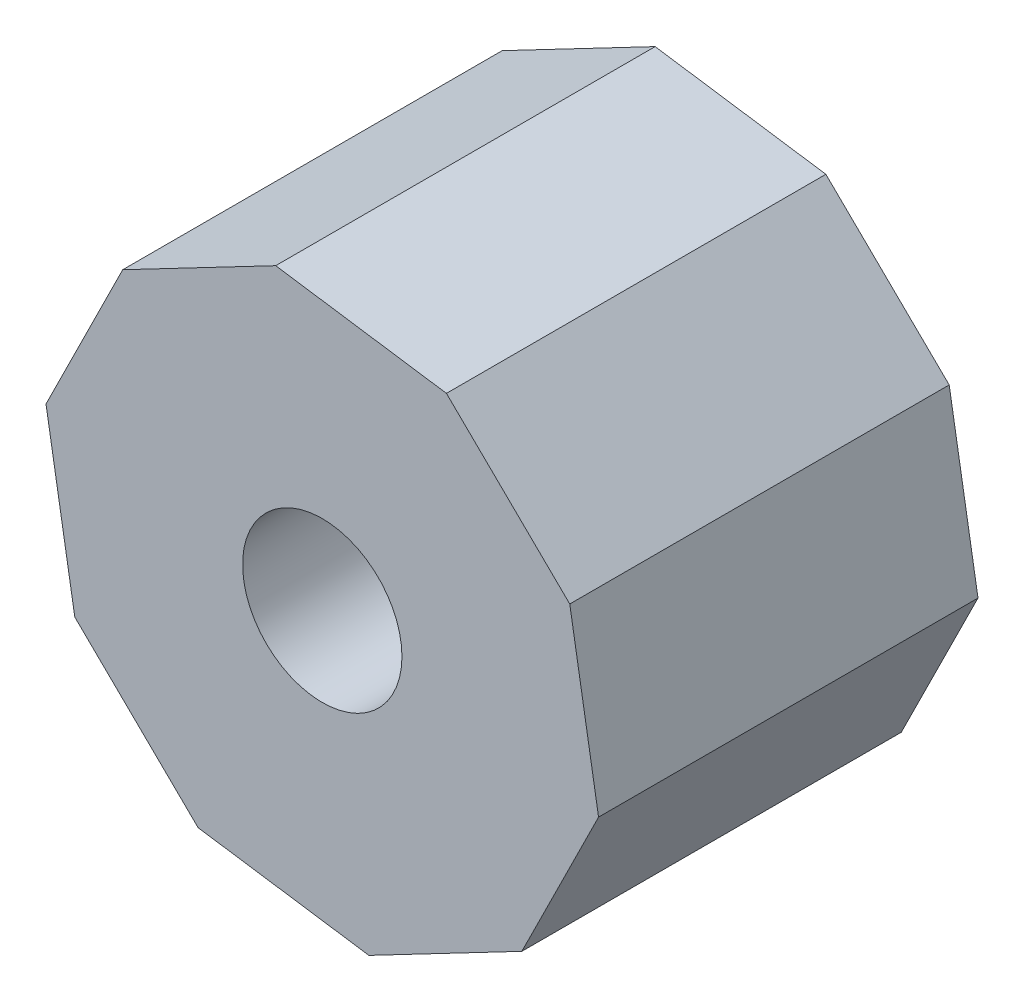
SolidWorks part; units mm, degrees
ref_plane "Plan de face" through (0, 0, 0) normal (0, 0, 1) x (1, 0, 0)
ref_plane "Plan de dessus" through (0, 0, 0) normal (0, 1, 0) x (1, 0, 0)
ref_plane "Plan de droite" through (0, 0, 0) normal (1, 0, 0) x (0, 0, -1)
sketch "Esquisse1" plane through (0, 0, 0) normal (0, 0, 1) x (1, 0, 0)
  line L0 (-5.2592, 5.1492) -> (-7.2814, 1.0745)
  line L1 (1.5094, -3.8112) -> (4.0553, -0.5985)
  line L2 (4.0553, -0.5985) -> (2.5459, 3.2127)
  line L3 (2.5459, 3.2127) -> (-1.5094, 3.8112)
  line L4 (-1.5094, 3.8112) -> (-4.0553, 0.5985)
  line L5 (-4.0553, 0.5985) -> (-2.5459, -3.2127)
  line L6 (-2.5459, -3.2127) -> (1.5094, -3.8112)
  line L7 (1.2281, -7.2571) -> (5.2592, -5.1492)
  line L8 (5.2592, -5.1492) -> (7.2814, -1.0745)
  line L9 (7.2814, -1.0745) -> (6.5224, 3.4106)
  line L10 (6.5224, 3.4106) -> (3.272, 6.5929)
  line L11 (3.272, 6.5929) -> (-1.2281, 7.2571)
  line L12 (-1.2281, 7.2571) -> (-5.2592, 5.1492)
  line L13 (-7.2814, 1.0745) -> (-6.5224, -3.4106)
  line L14 (-6.5224, -3.4106) -> (-3.272, -6.5929)
  line L15 (-3.272, -6.5929) -> (1.2281, -7.2571)
  circle A0 centre (0, 0) radius 3.55 construction
  circle A2 centre (0, 0) radius 7 construction
  dimension "D1" = 7.1
extrude "Boss.-Extru.1" add sketch "Esquisse1" along normal blind 10
sketch "Esquisse3" plane through (0, 0, 10) normal (0, 0, 1) x (1, 0, 0)
  circle A0 centre (0, 0) radius 2.1
  circle A1 centre (0, 0) radius 4.5179
  dimension "D1" = 4.2
extrude "Boss.-Extru.2" add sketch "Esquisse3" against normal blind 4
